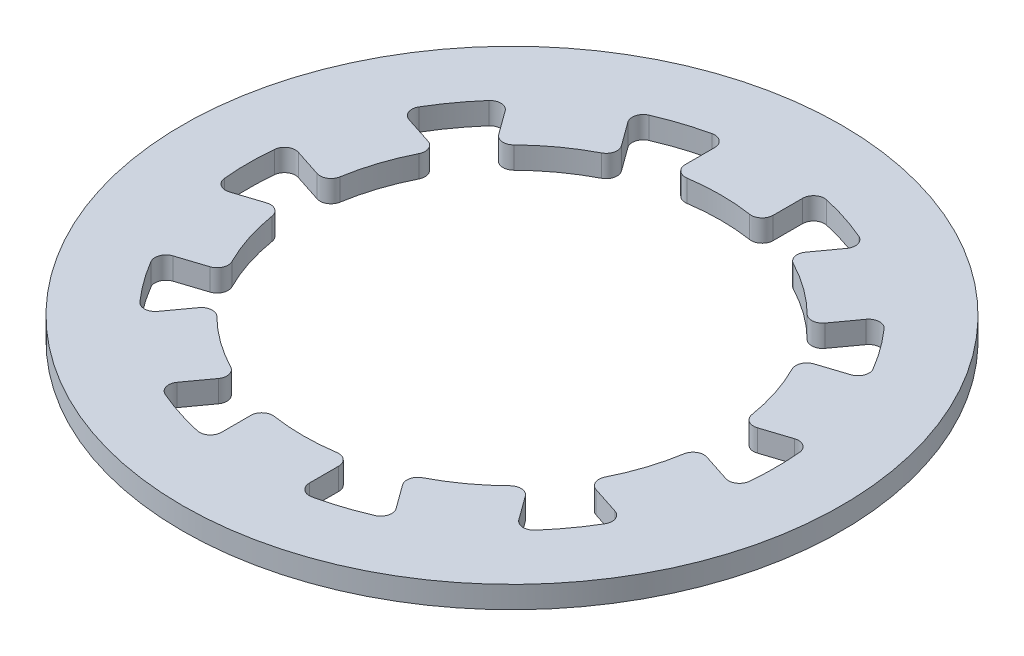
SolidWorks part; units mm, degrees
ref_plane "Front Plane" through (0, 0, 0) normal (0, 0, 1) x (1, 0, 0)
ref_plane "Top Plane" through (0, 0, 0) normal (0, 1, 0) x (1, 0, 0)
ref_plane "Right Plane" through (0, 0, 0) normal (1, 0, 0) x (0, 0, -1)
sketch "Sketch1" plane through (0, 0, 0) normal (0, 1, 0) x (1, 0, 0)
  line L0 (0, 18.9947) -> (0, -20.503) construction
  line L1 (-18.0992, 0) -> (25.0749, 0) construction
  line L2 (-2, 11.225) -> (-2, 9.8869)
  line L3 (2, 11.225) -> (2, 9.8869)
  line L4 (2, 18.9947) -> (2, -20.503) construction
  line L5 (-2, 18.9947) -> (-2, -20.503) construction
  line L6 (8.2159, 7.9056) -> (7.4294, 6.8231)
  line L7 (4.9798, 10.2568) -> (4.1933, 9.1742)
  line L8 (11.2936, 1.5666) -> (10.021, 1.1531)
  line L9 (10.0575, 5.3708) -> (8.7849, 4.9573)
  line L10 (10.0575, -5.3708) -> (8.7849, -4.9573)
  line L11 (11.2936, -1.5666) -> (10.021, -1.1531)
  line L12 (4.9798, -10.2568) -> (4.1933, -9.1742)
  line L13 (8.2159, -7.9056) -> (7.4294, -6.8231)
  line L14 (-2, -11.225) -> (-2, -9.8869)
  line L15 (2, -11.225) -> (2, -9.8869)
  line L16 (-8.2159, -7.9056) -> (-7.4294, -6.8231)
  line L17 (-4.9798, -10.2568) -> (-4.1933, -9.1742)
  line L18 (-11.2936, -1.5666) -> (-10.021, -1.1531)
  line L19 (-10.0575, -5.3708) -> (-8.7849, -4.9573)
  line L20 (-10.0575, 5.3708) -> (-8.7849, 4.9573)
  line L21 (-11.2936, 1.5666) -> (-10.021, 1.1531)
  line L22 (-4.9798, 10.2568) -> (-4.1933, 9.1742)
  line L23 (-8.2159, 7.9056) -> (-7.4294, 6.8231)
  circle A0 centre (0, 0) radius 15
  arc A1 (-4.3679, 8.4363) -> (-6.6736, 6.7611) centre (0, 0) ccw
  arc A2 (-8.9952, 7.9427) -> (-10.3336, 6.1005) centre (0, 0) ccw
  arc A3 (-8.4925, 4.2577) -> (-9.3732, 1.5472) centre (0, 0) ccw
  arc A4 (-9.3732, -1.5472) -> (-8.4925, -4.2577) centre (0, 0) ccw
  arc A5 (-6.6736, -6.7611) -> (-4.3679, -8.4363) centre (0, 0) ccw
  arc A6 (-1.425, -9.3925) -> (1.425, -9.3925) centre (0, 0) ccw
  arc A7 (4.3679, -8.4363) -> (6.6736, -6.7611) centre (0, 0) ccw
  arc A8 (8.4925, -4.2577) -> (9.3732, -1.5472) centre (0, 0) ccw
  arc A9 (9.3732, 1.5472) -> (8.4925, 4.2577) centre (0, 0) ccw
  arc A10 (6.6736, 6.7611) -> (4.3679, 8.4363) centre (0, 0) ccw
  arc A11 (1.425, 9.3925) -> (-1.425, 9.3925) centre (0, 0) ccw
  arc A12 (-11.9459, 1.1385) -> (-11.9459, -1.1385) centre (0, 0) ccw
  arc A13 (-10.3336, -6.1005) -> (-8.9952, -7.9427) centre (0, 0) ccw
  arc A14 (-4.7743, -11.0094) -> (-2.6087, -11.713) centre (0, 0) ccw
  arc A15 (2.6087, -11.713) -> (4.7743, -11.0094) centre (0, 0) ccw
  arc A16 (8.9952, -7.9427) -> (10.3336, -6.1005) centre (0, 0) ccw
  arc A17 (11.9459, -1.1385) -> (11.9459, 1.1385) centre (0, 0) ccw
  arc A18 (10.3336, 6.1005) -> (8.9952, 7.9427) centre (0, 0) ccw
  arc A19 (-2.6087, 11.713) -> (-4.7743, 11.0094) centre (0, 0) ccw
  arc A20 (4.7743, 11.0094) -> (2.6087, 11.713) centre (0, 0) ccw
  arc A21 (-11.2936, 1.5666) -> (-11.9459, 1.1385) centre (-11.4481, 1.0911) ccw
  arc A22 (-11.2936, -1.5666) -> (-11.9459, -1.1385) centre (-11.4481, -1.0911) cw
  arc A23 (-10.021, -1.1531) -> (-9.3732, -1.5472) centre (-9.8665, -1.6286) cw
  arc A24 (-8.7849, -4.9573) -> (-8.4925, -4.2577) centre (-8.9394, -4.4818) ccw
  arc A25 (-10.0575, -5.3708) -> (-10.3336, -6.1005) centre (-9.903, -5.8463) ccw
  arc A26 (-8.2159, -7.9056) -> (-8.9952, -7.9427) centre (-8.6204, -7.6117) cw
  arc A27 (-7.4294, -6.8231) -> (-6.6736, -6.7611) centre (-7.0249, -7.117) cw
  arc A28 (-4.1933, -9.1742) -> (-4.3679, -8.4363) centre (-4.5978, -8.8803) ccw
  arc A29 (-4.9798, -10.2568) -> (-4.7743, -11.0094) centre (-4.5753, -10.5507) ccw
  arc A30 (-2, -11.225) -> (-2.6087, -11.713) centre (-2.5, -11.225) cw
  arc A31 (-2, -9.8869) -> (-1.425, -9.3925) centre (-1.5, -9.8869) cw
  arc A32 (2, -9.8869) -> (1.425, -9.3925) centre (1.5, -9.8869) ccw
  arc A33 (2, -11.225) -> (2.6087, -11.713) centre (2.5, -11.225) ccw
  arc A34 (4.9798, -10.2568) -> (4.7743, -11.0094) centre (4.5753, -10.5507) cw
  arc A35 (4.1933, -9.1742) -> (4.3679, -8.4363) centre (4.5978, -8.8803) cw
  arc A36 (7.4294, -6.8231) -> (6.6736, -6.7611) centre (7.0249, -7.117) ccw
  arc A37 (8.2159, -7.9056) -> (8.9952, -7.9427) centre (8.6204, -7.6117) ccw
  arc A38 (10.0575, -5.3708) -> (10.3336, -6.1005) centre (9.903, -5.8463) cw
  arc A39 (8.7849, -4.9573) -> (8.4925, -4.2577) centre (8.9394, -4.4818) cw
  arc A40 (10.021, -1.1531) -> (9.3732, -1.5472) centre (9.8665, -1.6286) ccw
  arc A41 (11.2936, -1.5666) -> (11.9459, -1.1385) centre (11.4481, -1.0911) ccw
  arc A42 (11.2936, 1.5666) -> (11.9459, 1.1385) centre (11.4481, 1.0911) cw
  arc A43 (10.021, 1.1531) -> (9.3732, 1.5472) centre (9.8665, 1.6286) cw
  arc A44 (8.7849, 4.9573) -> (8.4925, 4.2577) centre (8.9394, 4.4818) ccw
  arc A45 (10.0575, 5.3708) -> (10.3336, 6.1005) centre (9.903, 5.8463) ccw
  arc A46 (8.2159, 7.9056) -> (8.9952, 7.9427) centre (8.6204, 7.6117) cw
  arc A47 (7.4294, 6.8231) -> (6.6736, 6.7611) centre (7.0249, 7.117) cw
  arc A48 (4.1933, 9.1742) -> (4.3679, 8.4363) centre (4.5978, 8.8803) ccw
  arc A49 (4.9798, 10.2568) -> (4.7743, 11.0094) centre (4.5753, 10.5507) ccw
  arc A50 (2, 11.225) -> (2.6087, 11.713) centre (2.5, 11.225) cw
  arc A51 (2, 9.8869) -> (1.425, 9.3925) centre (1.5, 9.8869) cw
  arc A52 (-2, 9.8869) -> (-1.425, 9.3925) centre (-1.5, 9.8869) ccw
  arc A53 (-2, 11.225) -> (-2.6087, 11.713) centre (-2.5, 11.225) ccw
  arc A54 (-7.4294, 6.8231) -> (-6.6736, 6.7611) centre (-7.0249, 7.117) ccw
  arc A55 (-4.1933, 9.1742) -> (-4.3679, 8.4363) centre (-4.5978, 8.8803) cw
  arc A56 (-4.9798, 10.2568) -> (-4.7743, 11.0094) centre (-4.5753, 10.5507) cw
  arc A57 (-10.021, 1.1531) -> (-9.3732, 1.5472) centre (-9.8665, 1.6286) ccw
  arc A58 (-8.7849, 4.9573) -> (-8.4925, 4.2577) centre (-8.9394, 4.4818) cw
  arc A59 (-8.2159, 7.9056) -> (-8.9952, 7.9427) centre (-8.6204, 7.6117) ccw
  arc A60 (-10.0575, 5.3708) -> (-10.3336, 6.1005) centre (-9.903, 5.8463) cw
  point P3 (0, 0)
  point P55 (0, 0)
  point P113 (2, 11.8322)
  point P116 (2, 9.2871)
  point P121 (-2, 11.8322)
  dimension "D1" = 30
  dimension "D2" = 19
  dimension "D5" = 24
  dimension "D7" = 0.5
  dimension "D3" = 2
  dimension "D4" = 2
  dimension "D6" = 10
extrude "Boss-Extrude1" add sketch "Sketch1" along normal blind 1
